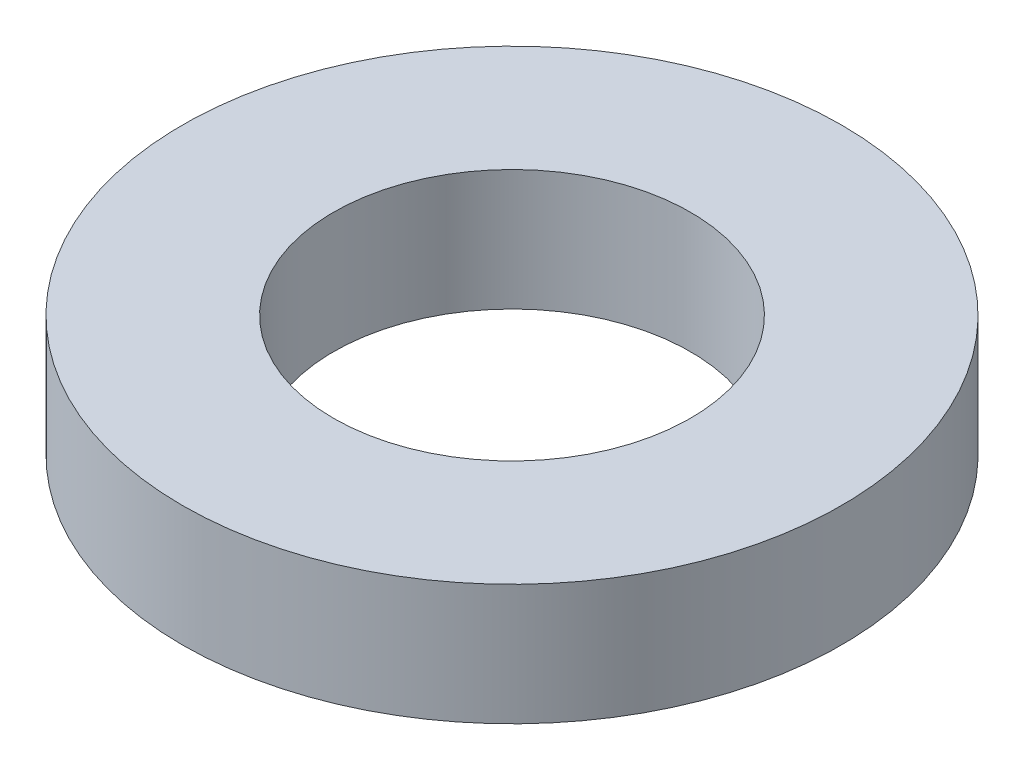
SolidWorks part; units mm, degrees
ref_plane "Front Plane" through (0, 0, 0) normal (0, 0, 1) x (1, 0, 0)
ref_plane "Top Plane" through (0, 0, 0) normal (0, 1, 0) x (1, 0, 0)
ref_plane "Right Plane" through (0, 0, 0) normal (1, 0, 0) x (0, 0, -1)
sketch "Sketch2" plane through (0, 0, 0) normal (0, 1, 0) x (1, 0, 0)
  circle A0 centre (0, 0) radius 32.5
  circle A1 centre (0, 0) radius 60
  dimension "D1" = 65
  dimension "D2" = 120
extrude "Boss-Extrude1" add sketch "Sketch2" along normal blind 22
